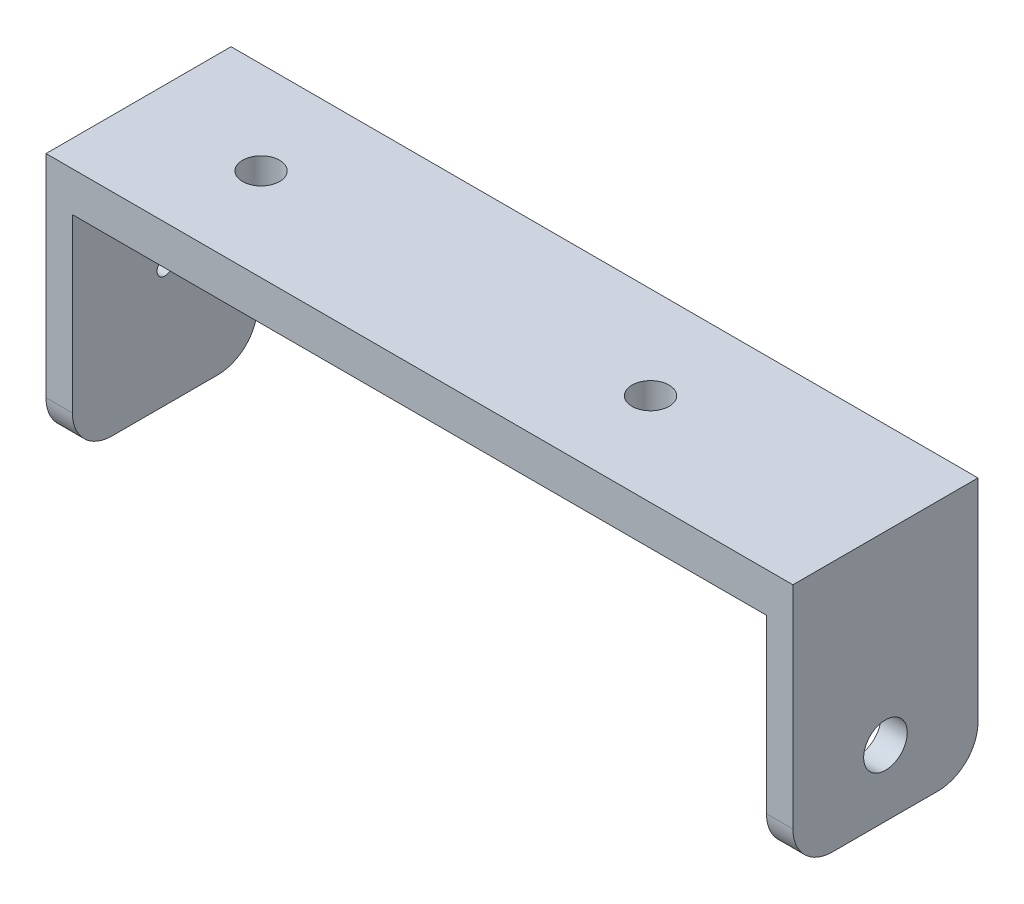
SolidWorks part; units mm, degrees
ref_plane "前视基准面" through (0, 0, 0) normal (0, 0, 1) x (1, 0, 0)
ref_plane "上视基准面" through (0, 0, 0) normal (0, 1, 0) x (1, 0, 0)
ref_plane "右视基准面" through (0, 0, 0) normal (1, 0, 0) x (0, 0, -1)
sketch "草图1" plane through (0, 0, 0) normal (0, 0, 1) x (1, 0, 0)
  line L0 (-28.25, 0) -> (-28.25, 19)
  line L1 (-28.25, 19) -> (28.25, 19)
  line L2 (28.25, 19) -> (28.25, 0)
  line L3 (28.25, 0) -> (26.25, 0)
  line L4 (26.25, 0) -> (26.25, 16)
  line L5 (26.25, 16) -> (-26.25, 16)
  line L6 (-26.25, 16) -> (-26.25, 0)
  line L7 (-26.25, 0) -> (-28.25, 0)
  line L8 (-61.4321, 26.241) -> (-59.0057, 26.241)
  line L9 (0, 0) -> (0, 21.894) construction
  dimension "D1" = 56.5
  dimension "D2" = 19
  dimension "D3" = 3
  dimension "D4" = 2
  dimension "D5" = 2
  dimension "D6" = 19
extrude "凸台-拉伸1" add sketch "草图1" along normal blind 14 contours L5 L9 L1 L0 L7 L6 | L9 L5 L4 L3 L2 L1
sketch "草图2" plane through (28.25, 0, 0) normal (1, 0, 0) x (0, 0, -1)
  line L0 (-7, 0) -> (-7, 19) construction
  line L1 (-14, 0) -> (0, 0) construction
  line L2 (-14, 19) -> (0, 19) construction
  circle A0 centre (-7, 5) radius 1.65
  dimension "D2" = 3.3
  dimension "D1" = 5
extrude "切除-拉伸1" cut sketch "草图2" against normal up to surface (2 mm away) up to face at (26.25, 8, 7)
sketch "草图3" plane through (0, 19, 0) normal (0, 1, 0) x (1, 0, 0)
  line L0 (-28.25, -7) -> (28.25, -7) construction
  line L1 (-28.25, -14) -> (-28.25, 0) construction
  line L2 (28.25, -14) -> (28.25, 0) construction
  line L3 (0, 0) -> (0, -14) construction
  line L4 (-28.25, 0) -> (28.25, 0) construction
  line L5 (-28.25, -14) -> (28.25, -14) construction
  line L6 (-4.25, 0) -> (-4.25, -14) construction
  circle A0 centre (-18.98, -7) radius 1.4
  circle A1 centre (10.48, -7) radius 1.4
  dimension "D2" = 2.8
  dimension "D1" = 29.46
  dimension "D3" = 4.25
extrude "切除-拉伸2" cut sketch "草图3" against normal blind 14
fillet "圆角1" radius 3 4 edges at (27.25, 0, 0) (27.25, 0, 14) (-27.25, 0, 0) (-27.25, 0, 14)
sketch "草图5" plane through (-28.25, 0, 0) normal (-1, 0, 0) x (0, 0, 1)
  line L0 (7, 5) -> (7, 20.3188) construction
  circle A0 centre (7, 5) radius 1.65 construction
  circle A1 centre (7, 5) radius 1.65 construction
  circle A2 centre (7, 9.085) radius 0.6
  circle A3 centre (7, 13.085) radius 0.6
  point P8 (0, 0)
  point P9 (0, 0)
  dimension "D1" = 1.2
  dimension "D2" = 4.085
  dimension "D3" = 8.085
extrude "切除-拉伸3" cut sketch "草图5" against normal blind 10
